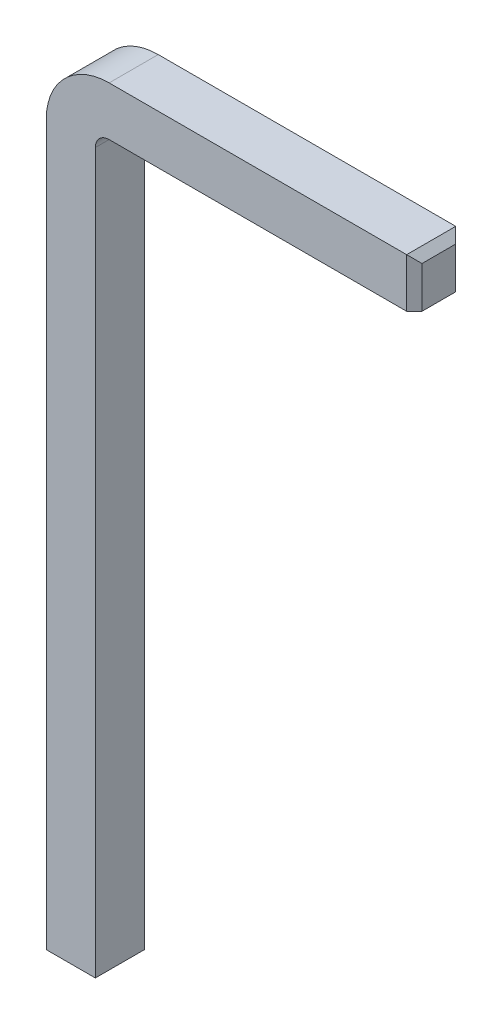
SolidWorks part; units mm, degrees
ref_plane "Front" through (0, 0, 0) normal (0, 0, 1) x (1, 0, 0)
ref_plane "Top" through (0, 0, 0) normal (0, 1, 0) x (1, 0, 0)
ref_plane "Right" through (0, 0, 0) normal (1, 0, 0) x (0, 0, -1)
sketch "Эскиз1" plane through (0, 0, 0) normal (0, 1, 0) x (1, 0, 0)
  line L1 (-0.32, 0.32) -> (0.32, 0.32)
  line L2 (-0.32, 0.32) -> (-0.32, -0.32)
  line L3 (-0.32, -0.32) -> (0.32, -0.32)
  line L4 (0.32, 0.32) -> (0.32, -0.32)
  line L5 (-0.32, 0.32) -> (0.32, -0.32) construction
  line L6 (-0.32, -0.32) -> (0.32, 0.32) construction
  point P0 (0, 0)
  dimension "D1" = 0.64
  dimension "D2" = 0.64
sketch "Эскиз2" plane through (0, 0, 0) normal (0, 0, 1) x (1, 0, 0)
  line L0 (0, 0) -> (0, 9.48)
  line L1 (0.5, 9.98) -> (4.48, 9.98)
  arc A0 (0, 9.48) -> (0.5, 9.98) centre (0.5, 9.48) cw
  point P6 (0, 9.98)
  dimension "D3" = 0.5
  dimension "D1" = 9.98
  dimension "D2" = 4.48
sweep "По траектории1" add profiles "Эскиз1" path "Эскиз2"
chamfer "Фаска1" distance 0.1 angle 45 7 edges at (0, 0, 0.32) (0, 0, -0.32) (-0.32, 0, 0) (0.32, 0, 0) (4.48, 9.98, -0.32) (4.48, 9.98, 0.32) (4.48, 10.3, 0)
equation "\"D2@Эскиз1\"=\"D1@Эскиз1\""
